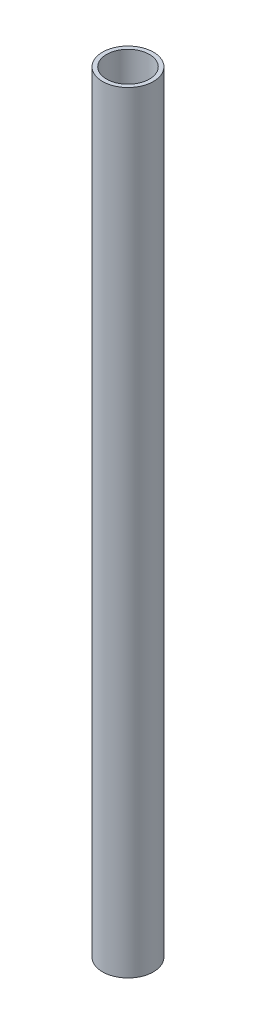
SolidWorks part; units mm, degrees
ref_plane "Front Plane" through (0, 0, 0) normal (0, 0, 1) x (1, 0, 0)
ref_plane "Top Plane" through (0, 0, 0) normal (0, 1, 0) x (1, 0, 0)
ref_plane "Right Plane" through (0, 0, 0) normal (1, 0, 0) x (0, 0, -1)
sketch "Sketch2" plane through (0, 0, 0) normal (0, 1, 0) x (1, 0, 0)
  circle A0 centre (0, 0) radius 25.4
  circle A1 centre (0, 0) radius 30.1625
extrude "Boss-Extrude1" add sketch "Sketch2" along normal blind 914.4
